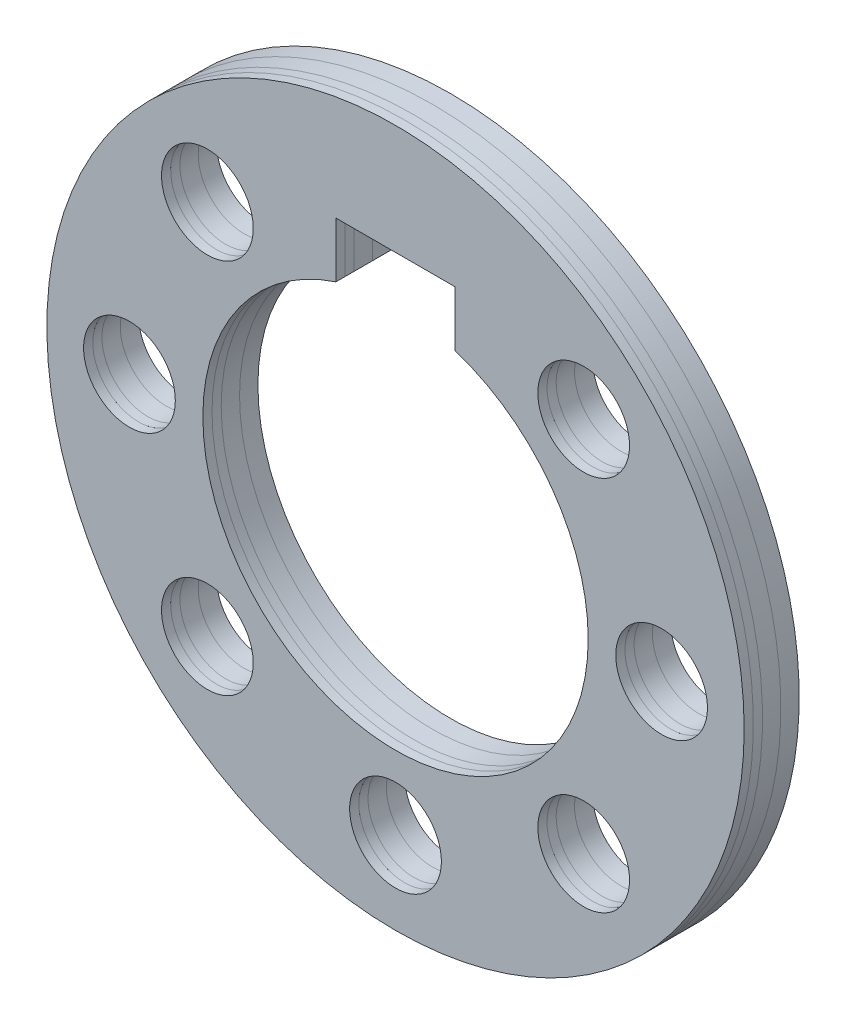
SolidWorks part; units mm, degrees
material "Ст 3 ГОСТ 380-2005"
ref_plane "Спереди" through (0, 0, 0) normal (0, 0, 1) x (1, 0, 0)
ref_plane "Сверху" through (0, 0, 0) normal (0, 1, 0) x (1, 0, 0)
ref_plane "Слева" through (0, 0, 0) normal (1, 0, 0) x (0, 0, -1)
sketch "Эскиз1" plane through (0, 0, 0) normal (0, 0, 1) x (1, 0, 0)
  line L0 (0, 13) -> (0, 0) construction
  line L1 (-3.25, 13) -> (3.25, 13)
  line L2 (-3.25, 13) -> (-3.25, 9.9844)
  line L4 (3.25, 13) -> (3.25, 9.9844)
  circle A0 centre (0, 0) radius 19
  arc A1 (-3.25, 9.9844) -> (3.25, 9.9844) centre (0, 0) ccw
  dimension "D1" = 38
  dimension "D2" = 21
  dimension "D3" = 6.5
  dimension "D4" = 13
extrude "Вытянуть1" add sketch "Эскиз1" along normal blind 5
sketch "Эскиз2" plane through (0, 0, 5) normal (0, 0, 1) x (1, 0, 0)
  line L1 (0, -14.5) -> (10.253, -10.253) construction
  line L2 (10.253, -10.253) -> (14.5, 0) construction
  line L3 (14.5, 0) -> (10.253, 10.253) construction
  line L4 (10.253, 10.253) -> (0, 14.5) construction
  line L5 (0, 14.5) -> (-10.253, 10.253) construction
  line L6 (-10.253, 10.253) -> (-14.5, 0) construction
  line L7 (-14.5, 0) -> (-10.253, -10.253) construction
  line L8 (-10.253, -10.253) -> (0, -14.5) construction
  circle A0 centre (0, 0) radius 14.5 construction
  circle A1 centre (10.253, 10.253) radius 2.5
  circle A2 centre (14.5, 0) radius 2.5
  circle A3 centre (10.253, -10.253) radius 2.5
  circle A4 centre (0, -14.5) radius 2.5
  circle A5 centre (-10.253, -10.253) radius 2.5
  circle A6 centre (-14.5, 0) radius 2.5
  circle A7 centre (-10.253, 10.253) radius 2.5
  arc A8 (-3.25, 9.9844) -> (3.25, 9.9844) centre (0, 0) ccw construction
  dimension "D1" = 29
  dimension "D2" = 5
  dimension "D3" = 1.5
extrude "Вытянуть2" cut sketch "Эскиз2" against normal through all
sketch "Эскиз3" plane through (0, 0, 0) normal (1, 0, 0) x (0, 0, -1)
  line L0 (-4.5, 19) -> (-4.5, -19)
  line L1 (0, 19) -> (-5, 19) construction
  line L2 (-5, -19) -> (0, -19) construction
  line L3 (-4, 19) -> (-4, -19)
  line L4 (-3, 19) -> (-3, -19)
  line L5 (-2, 19) -> (-2, -19)
  line L6 (0, -19) -> (0, 19) construction
  line L7 (-5, 19) -> (-5, -19) construction
  dimension "D1" = 2
  dimension "D2" = 0.5
  dimension "D3" = 0.5
  dimension "D4" = 1
  dimension "D5" = 1
split "Разделить1" trim tools "Эскиз3" bodies to split 102 resulting bodies 103 104 105 106 107
delete or keep bodies "Тело-Удалить1" type delete bodies bodies 107
